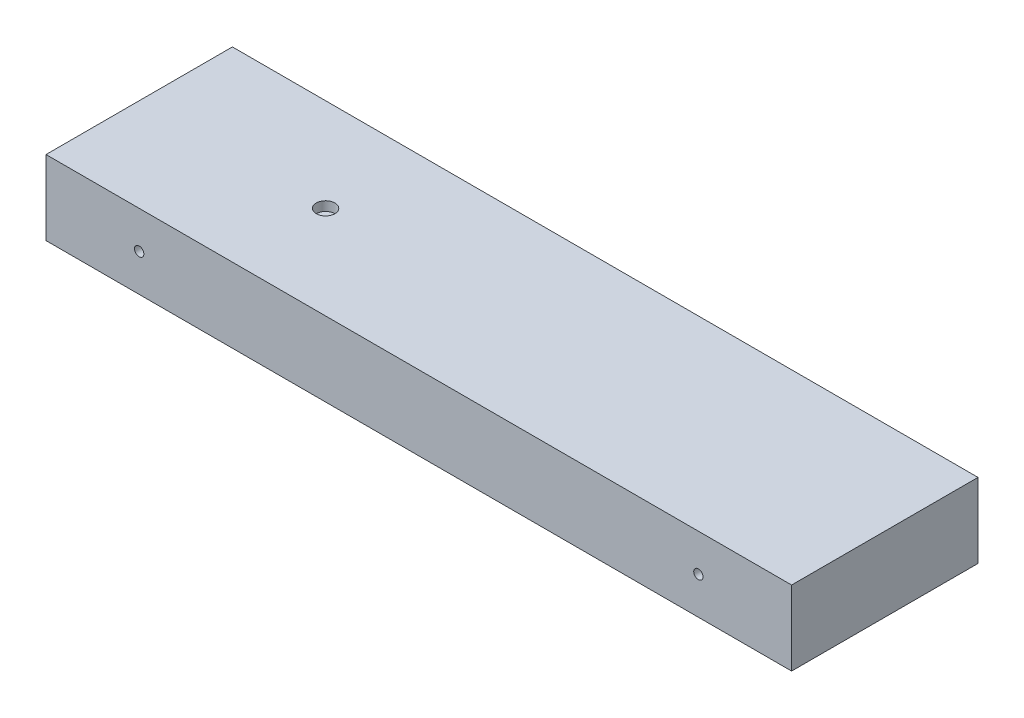
SolidWorks part; units mm, degrees
ref_plane "Front Plane" through (0, 0, 0) normal (0, 0, 1) x (1, 0, 0)
ref_plane "Top Plane" through (0, 0, 0) normal (0, 1, 0) x (1, 0, 0)
ref_plane "Right Plane" through (0, 0, 0) normal (1, 0, 0) x (0, 0, -1)
sketch "Sketch1" plane through (0, 0, 0) normal (0, 1, 0) x (1, 0, 0)
  line L1 (0, 0) -> (800, 0)
  line L2 (0, 0) -> (0, 200)
  line L3 (0, 200) -> (800, 200)
  line L4 (800, 0) -> (800, 200)
  dimension "D1" = 800
  dimension "D2" = 200
extrude "Boss-Extrude1" add sketch "Sketch1" along normal blind 80
sketch "Sketch3" plane through (0, 0, 0) normal (0, 0, 1) x (1, 0, 0)
  line L0 (0, 80) -> (800, 80) construction
  line L3 (0, 80) -> (0, 0) construction
  circle A0 centre (100, 40) radius 5
  circle A1 centre (700, 40) radius 5
  dimension "D4" = 10
  dimension "D5" = 10
  dimension "D1" = 40
  dimension "D2" = 40
  dimension "D3" = 700
  dimension "D6" = 100
extrude "Cut-Extrude2" cut sketch "Sketch3" against normal blind 200
sketch "Sketch4" plane through (0, 80, 0) normal (0, 1, 0) x (1, 0, 0)
  line L0 (0, 200) -> (0, 0) construction
  line L1 (800, 200) -> (0, 200) construction
  circle A0 centre (200, 100) radius 10
  point P2 (0, 0)
  dimension "D1" = 20
  dimension "D2" = 200
  dimension "D3" = 100
extrude "Cut-Extrude3" cut sketch "Sketch4" against normal blind 10
